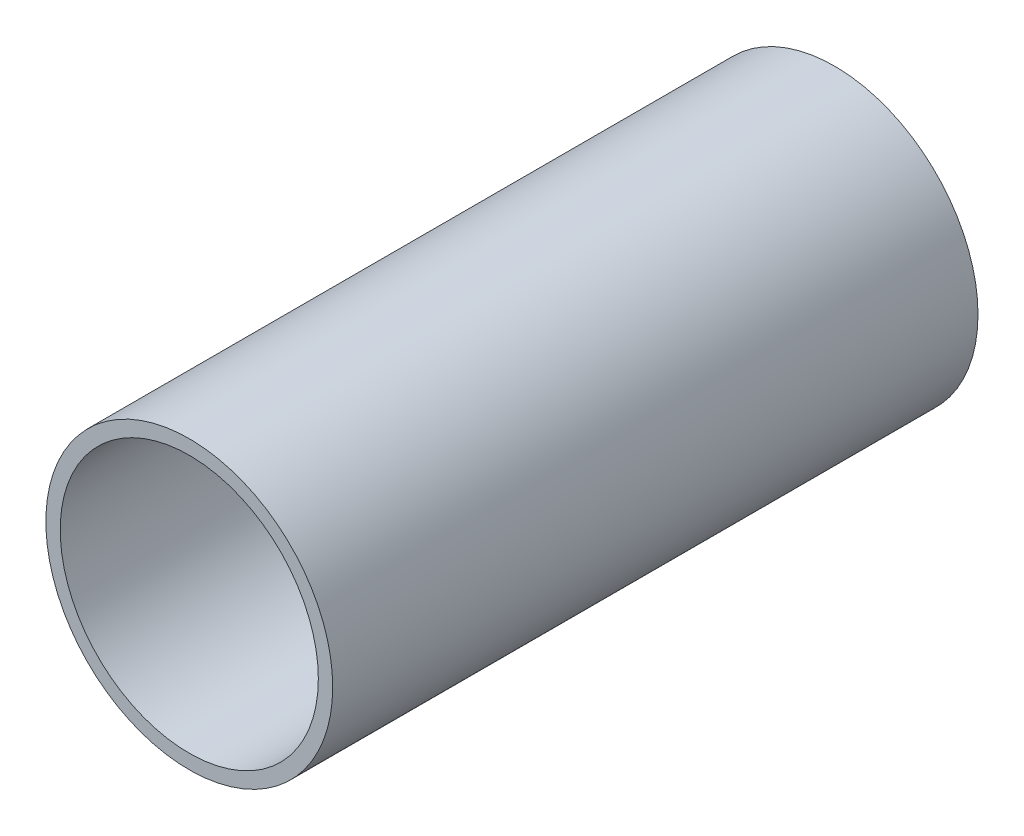
SolidWorks part; units mm, degrees
material "Ductile Iron"
ref_plane "Front Plane" through (0, 0, 0) normal (0, 0, 1) x (1, 0, 0)
ref_plane "Top Plane" through (0, 0, 0) normal (0, 1, 0) x (1, 0, 0)
ref_plane "Right Plane" through (0, 0, 0) normal (1, 0, 0) x (0, 0, -1)
sketch "Sketch1" plane through (0, 0, 0) normal (0, 0, 1) x (1, 0, 0)
  circle A0 centre (0, 0) radius 22.225
  circle A1 centre (0, 0) radius 20
  dimension "D1" = 44.45
  dimension "D2" = 40
extrude "Boss-Extrude1" add sketch "Sketch1" along normal blind 100
